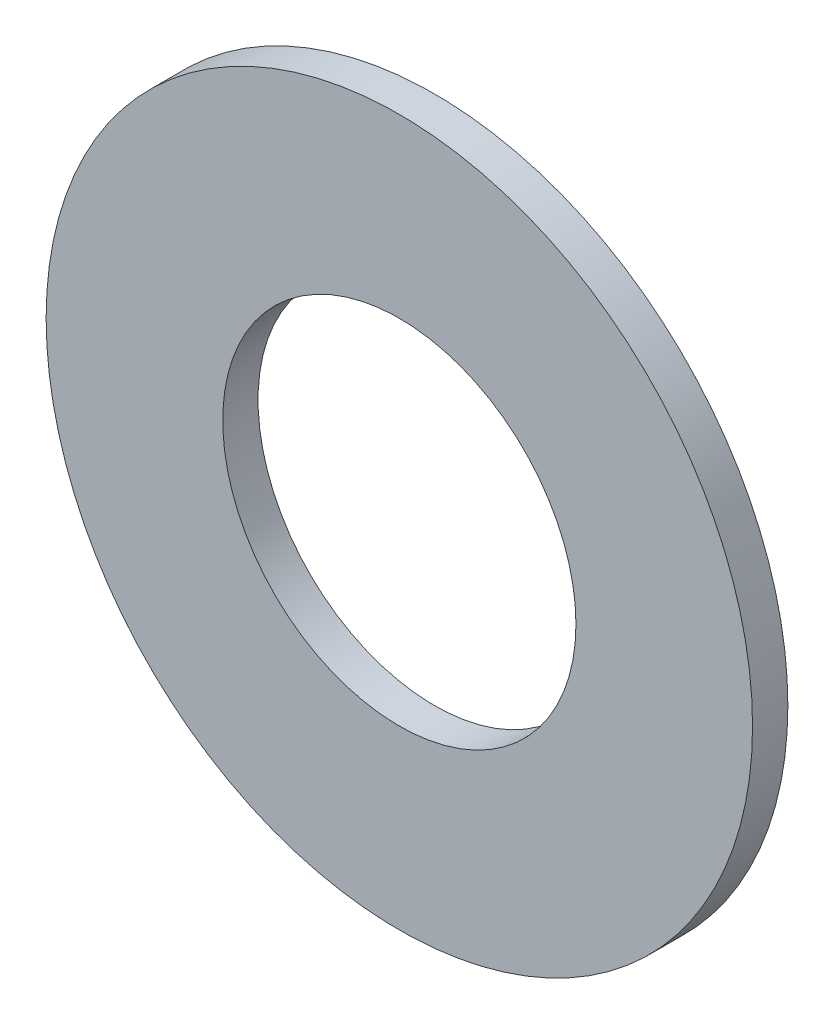
SolidWorks part; units mm, degrees
ref_plane "Front Plane" through (0, 0, 0) normal (0, 0, 1) x (1, 0, 0)
ref_plane "Top Plane" through (0, 0, 0) normal (0, 1, 0) x (1, 0, 0)
ref_plane "Right Plane" through (0, 0, 0) normal (1, 0, 0) x (0, 0, -1)
sketch "Sketch1" plane through (0, 0, 0) normal (0, 0, 1) x (1, 0, 0)
  circle A0 centre (0, 0) radius 10
extrude "Boss-Extrude1" add sketch "Sketch1" along normal blind 1
sketch "Sketch2" plane through (0, 0, 1) normal (0, 0, 1) x (1, 0, 0)
  circle A0 centre (0, 0) radius 5
extrude "Cut-Extrude1" cut sketch "Sketch2" against normal blind 4
